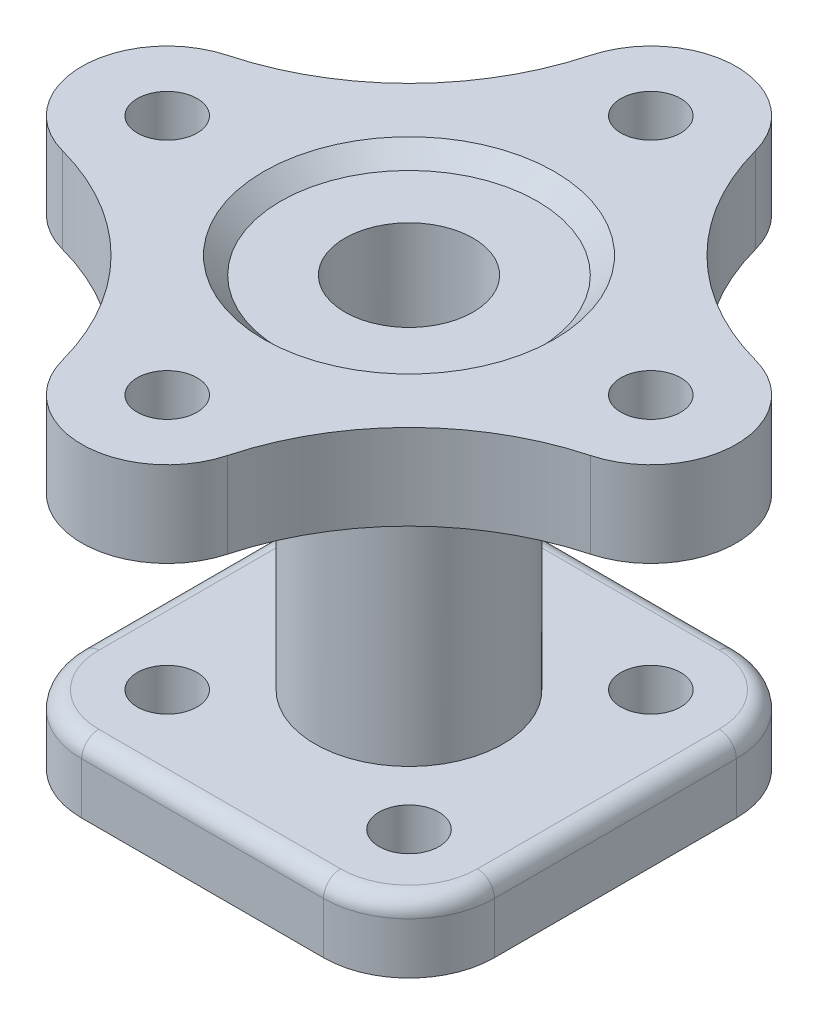
SolidWorks part; units mm, degrees
material "1060 Alloy"
ref_plane "Front Plane" through (0, 0, 0) normal (0, 0, 1) x (1, 0, 0)
ref_plane "Top Plane" through (0, 0, 0) normal (0, 1, 0) x (1, 0, 0)
ref_plane "Right Plane" through (0, 0, 0) normal (1, 0, 0) x (0, 0, -1)
sketch "Sketch1" plane through (0, 0, 0) normal (0, 1, 0) x (1, 0, 0)
  line L0 (0, 0) -> (0, 45.3799) construction
  line L1 (-17.9605, -30.6605) -> (17.9605, -30.6605)
  line L2 (-30.6605, -17.9605) -> (-30.6605, 17.9605)
  line L3 (-17.9605, 30.6605) -> (17.9605, 30.6605)
  line L4 (30.6605, -17.9605) -> (30.6605, 17.9605)
  line L5 (-30.6605, -30.6605) -> (30.6605, 30.6605) construction
  line L6 (-30.6605, 30.6605) -> (30.6605, -30.6605) construction
  line L7 (-37.9256, 0) -> (42.1105, 0) construction
  arc A0 (-17.9605, -30.6605) -> (-30.6605, -17.9605) centre (-17.9605, -17.9605) cw
  arc A1 (17.9605, -30.6605) -> (30.6605, -17.9605) centre (17.9605, -17.9605) ccw
  arc A2 (17.9605, 30.6605) -> (30.6605, 17.9605) centre (17.9605, 17.9605) cw
  arc A3 (-30.6605, 17.9605) -> (-17.9605, 30.6605) centre (-17.9605, 17.9605) cw
  circle A4 centre (-17.9605, 17.9605) radius 4.445
  circle A5 centre (17.9605, 17.9605) radius 4.445
  circle A6 centre (-17.9605, -17.9605) radius 4.445
  circle A7 centre (17.9605, -17.9605) radius 4.445
  point P0 (0, 0)
  dimension "D1" = 12.7
  dimension "D2" = 8.89
  dimension "D3" = 8.89
  dimension "D5" = 8.89
  dimension "D6" = 8.89
  dimension "D4" = 35.9209
  dimension "D7" = 35.9209
extrude "Boss-Extrude1" add sketch "Sketch1" along normal blind 10.16
fillet "Fillet1" radius 2.54 8 edges at (-26.9407, 10.16, 26.9407) (0, 10.16, 30.6605) (26.9407, 10.16, 26.9407) (30.6605, 10.16, 0) (26.9407, 10.16, -26.9407) (0, 10.16, -30.6605) (-26.9407, 10.16, -26.9407) (-30.6605, 10.16, 0)
sketch "Sketch2" plane through (0, 10.16, 0) normal (0, 1, 0) x (1, 0, 0)
  circle A0 centre (0, 0) radius 13.97
  dimension "D1" = 27.94
extrude "Boss-Extrude2" add sketch "Sketch2" along normal blind 43.18
sketch "Sketch10" plane through (0, 53.34, 0) normal (0, 1, 0) x (1, 0, 0)
  line L0 (-22.4055, -17.9605) -> (-13.5155, -17.9605) construction
  line L1 (-17.9605, -13.5155) -> (-17.9605, -22.4055) construction
  line L2 (-17.9605, 22.4055) -> (-17.9605, 13.5155) construction
  line L3 (-22.4055, 17.9605) -> (-13.5155, 17.9605) construction
  line L4 (0, 0) -> (-29.0435, -29.0435) construction
  line L5 (-29.0435, -29.0435) -> (26.9407, 26.9407) construction
  line L6 (-26.9407, 26.9407) -> (26.9407, -26.9407) construction
  circle A0 centre (-35.921, 0) radius 4.445
  circle A2 centre (-17.9605, -17.9605) radius 4.445 construction
  circle A3 centre (-17.9605, 17.9605) radius 4.445 construction
  arc A4 (30.6605, 17.9605) -> (17.9605, 30.6605) centre (17.9605, 17.9605) ccw construction
  arc A5 (-17.9605, 30.6605) -> (-30.6605, 17.9605) centre (-17.9605, 17.9605) ccw construction
  arc A6 (17.9605, -30.6605) -> (30.6605, -17.9605) centre (17.9605, -17.9605) ccw construction
  arc A7 (-39.208, 12.2673) -> (-39.208, -12.2673) centre (-35.921, 0) ccw
  arc A8 (-12.2673, 39.208) -> (12.2673, 39.208) centre (0, 35.921) cw
  circle A9 centre (0, 35.921) radius 4.445
  arc A10 (39.208, -12.2673) -> (39.208, 12.2673) centre (35.921, 0) ccw
  circle A11 centre (35.921, 0) radius 4.445
  arc A12 (12.2673, -39.208) -> (-12.2673, -39.208) centre (0, -35.921) cw
  circle A13 centre (0, -35.921) radius 4.445
  arc A15 (-39.208, 12.2673) -> (-12.2673, 39.208) centre (-49.069, 49.069) ccw
  arc A16 (-12.2673, -39.208) -> (-39.208, -12.2673) centre (-49.069, -49.069) ccw
  arc A17 (39.208, 12.2673) -> (12.2673, 39.208) centre (49.069, 49.069) cw
  arc A18 (12.2673, -39.208) -> (39.208, -12.2673) centre (49.069, -49.069) cw
  point P17 (-17.9605, -17.9605)
  point P18 (-17.9605, 17.9605)
  dimension "D1" = 8.89
  dimension "D4" = 25.4
  dimension "D5" = 76.2
  dimension "D6" = 76.2
  dimension "D2" = 25.4
  dimension "D3" = 25.4
extrude "Boss-Extrude3" add sketch "Sketch10" along normal blind 12.7
sketch "Sketch11" plane through (0, 66.04, 0) normal (0, 1, 0) x (1, 0, 0)
  circle A0 centre (0, 0) radius 9.525
  dimension "D1" = 19.05
extrude "Cut-Extrude1" cut sketch "Sketch11" against normal through all
sketch "Sketch12" plane through (0, 66.04, 0) normal (0, 1, 0) x (1, 0, 0)
  circle A0 centre (0, 0) radius 19.05
  dimension "D1" = 38.1
sketch "Sketch13" plane through (0, 0, 0) normal (0, 0, 1) x (1, 0, 0)
  line L0 (21.59, 66.04) -> (19.05, 63.5)
  line L1 (19.05, 66.04) -> (-19.05, 66.04) construction
  line L2 (39.208, 66.04) -> (12.2673, 66.04) construction
  line L3 (19.05, 63.5) -> (0, 63.5)
  line L5 (0, 63.5) -> (0, 66.04)
  line L6 (0, 66.04) -> (21.59, 66.04)
  dimension "D1" = 2.54
  dimension "D2" = 19.05
  dimension "D3" = 135
revolve "Cut-Revolve1" cut sketch "Sketch13" angle 360 about L5
